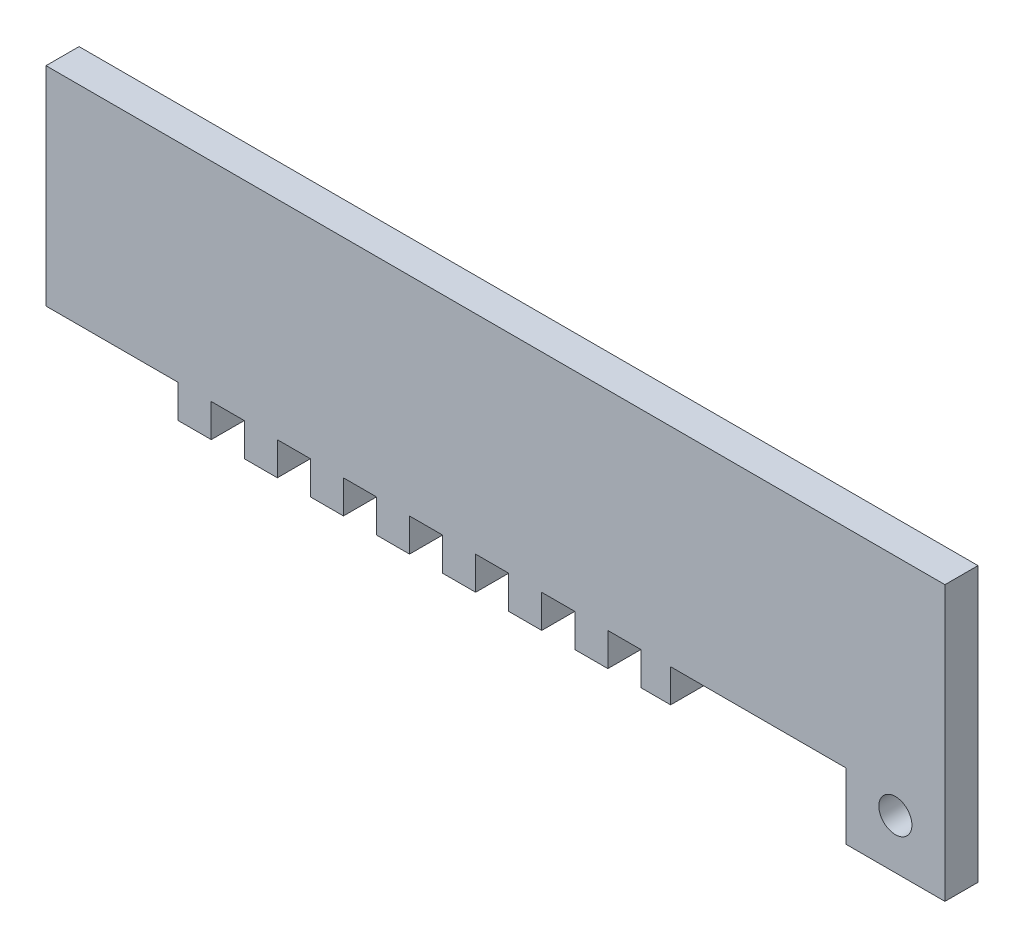
SolidWorks part; units mm, degrees
ref_plane "Plan de face" through (0, 0, 0) normal (0, 0, 1) x (1, 0, 0)
ref_plane "Plan de dessus" through (0, 0, 0) normal (0, 1, 0) x (1, 0, 0)
ref_plane "Plan de droite" through (0, 0, 0) normal (1, 0, 0) x (0, 0, -1)
sketch "Esquisse1" plane through (0, 0, 0) normal (0, 0, 1) x (1, 0, 0)
  line L1 (0, 0) -> (-189, 0)
  line L2 (0, 0) -> (0, 73)
  line L3 (0, 73) -> (-189, 73)
  line L4 (-189, 0) -> (-189, 73)
  dimension "D1" = 73
  dimension "D2" = 189
extrude "Boss.-Extru.1" add sketch "Esquisse1" along normal blind 10
sketch "Esquisse2" plane through (0, 0, 10) normal (0, 0, 1) x (1, 0, 0)
  line L2 (-189, 0) -> (0, 0) construction
  line L3 (-189, 73) -> (-189, 0) construction
  line L5 (-159, 0) -> (-149, 0)
  line L6 (-159, 0) -> (-159, 10)
  line L7 (-159, 10) -> (-149, 10)
  line L8 (-149, 0) -> (-149, 10)
  dimension "D1" = 30
  dimension "D3" = 10
  dimension "D4" = 10
extrude "Enlèv. mat.-Extru.2" cut sketch "Esquisse2" against normal blind 10
pattern_linear "Répétition linéaire2" count 8 spacing 20 along (1, 0, 0) of "Enlèv. mat.-Extru.2"
sketch "Esquisse3" plane through (0, 0, 10) normal (0, 0, 1) x (1, 0, 0)
  line L1 (-189, 0) -> (-159, 0)
  line L2 (-189, 0) -> (-189, 10)
  line L3 (-189, 10) -> (-159, 10)
  line L4 (-159, 0) -> (-159, 10)
extrude "Enlèv. mat.-Extru.3" cut sketch "Esquisse3" against normal blind 10
sketch "Esquisse4" plane through (0, 0, 0) normal (1, 0, 0) x (0, 0, -1)
  line L0 (0, 0) -> (0, 73) construction
  line L1 (-10, 73) -> (0, 73)
  line L2 (-10, 73) -> (-10, 10)
  line L3 (-10, 10) -> (0, 10)
  line L4 (0, 73) -> (0, 10)
  line L6 (-10, 0) -> (0, 0) construction
  dimension "D1" = 10
extrude "Boss.-Extru.2" add sketch "Esquisse4" along normal blind 83
sketch "Esquisse5" plane through (0, 10, 0) normal (0, -1, 0) x (1, 0, 0)
  line L0 (83, 10) -> (0, 10) construction
  line L1 (83, 0) -> (53, 0)
  line L2 (83, 0) -> (83, 10)
  line L3 (83, 10) -> (53, 10)
  line L4 (53, 0) -> (53, 10)
  dimension "D1" = 30
extrude "Boss.-Extru.3" add sketch "Esquisse5" along normal blind 20
sketch "Esquisse6" plane through (0, 0, 10) normal (0, 0, 1) x (1, 0, 0)
  line L0 (53, 10) -> (0, 10) construction
  line L1 (83, 73) -> (83, -10) construction
  circle A0 centre (68, 5) radius 5
  dimension "D1" = 10
  dimension "D2" = 15
extrude "Enlèv. mat.-Extru.4" cut sketch "Esquisse6" against normal blind 10
